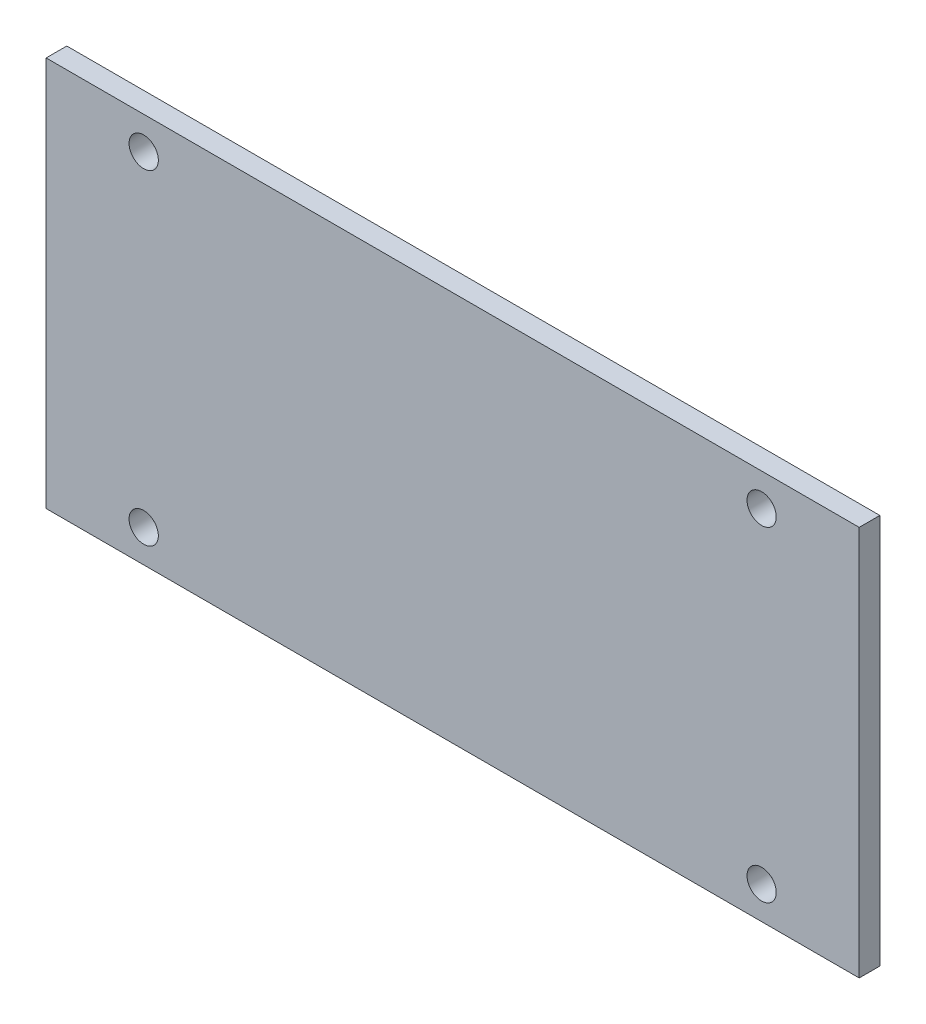
SolidWorks part; units mm, degrees
material "Acrylic (Medium-high impact)"
ref_plane "Plan de face" through (0, 0, 0) normal (0, 0, 1) x (1, 0, 0)
ref_plane "Plan de dessus" through (0, 0, 0) normal (0, 1, 0) x (1, 0, 0)
ref_plane "Plan de droite" through (0, 0, 0) normal (1, 0, 0) x (0, 0, -1)
sketch "Sketch1" plane through (0, 0, 0) normal (0, 0, 1) x (1, 0, 0)
  line L1 (62.5, -30) -> (-62.5, -30)
  line L2 (62.5, -30) -> (62.5, 30)
  line L3 (62.5, 30) -> (-62.5, 30)
  line L4 (-62.5, -30) -> (-62.5, 30)
  line L5 (62.5, -30) -> (-62.5, 30) construction
  line L6 (62.5, 30) -> (-62.5, -30) construction
  point P0 (0, 0)
  dimension "D1" = 125
  dimension "D2" = 60
extrude "Boss-Extrude1" add sketch "Sketch1" along normal blind 3.175
sketch "Sketch2" plane through (0, 0, 3.175) normal (0, 0, 1) x (1, 0, 0)
  line L0 (0, -30) -> (0, 30) construction
  line L1 (-62.5, -30) -> (62.5, -30) construction
  line L2 (62.5, 30) -> (-62.5, 30) construction
  line L3 (-62.5, 30) -> (-62.5, -30) construction
  circle A0 centre (-47.5, 25) radius 2.25
  circle A1 centre (-47.5, -25) radius 2.25
  circle A4 centre (47.5, -25) radius 2.25
  circle A5 centre (47.5, 25) radius 2.25
  dimension "D5" = 4.5
  dimension "D6" = 4.5
  dimension "D1" = 5
  dimension "D2" = 15
  dimension "D3" = 15
  dimension "D4" = 5
extrude "Cut-Extrude2" cut sketch "Sketch2" against normal blind 3.175
